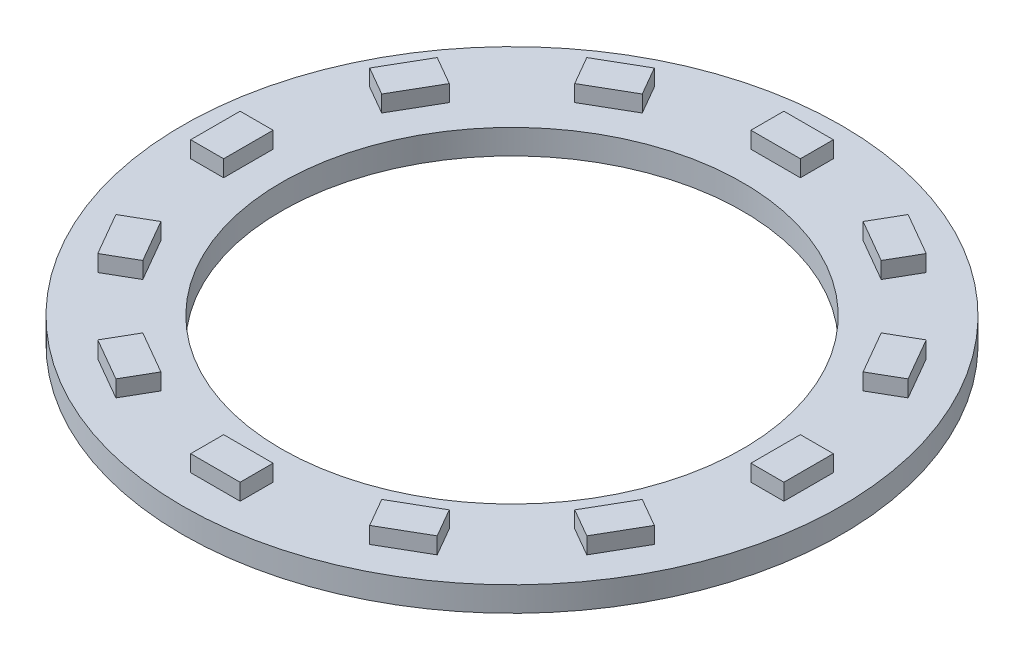
SolidWorks part; units mm, degrees
ref_plane "Front Plane" through (0, 0, 0) normal (0, 0, 1) x (1, 0, 0)
ref_plane "Top Plane" through (0, 0, 0) normal (0, 1, 0) x (1, 0, 0)
ref_plane "Right Plane" through (0, 0, 0) normal (1, 0, 0) x (0, 0, -1)
sketch "Sketch1" plane through (0, 0, 0) normal (0, 1, 0) x (1, 0, 0)
  circle A0 centre (0, 0) radius 20
  circle A1 centre (0, 0) radius 14
  dimension "D1" = 40
  dimension "D2" = 6
extrude "Boss-Extrude1" add sketch "Sketch1" along normal blind 1.5
sketch "Sketch2" plane through (0, 1.5, 0) normal (0, 1, 0) x (1, 0, 0)
  line L0 (0, 0) -> (0, 16) construction
  line L1 (-1.5, 18) -> (1.5, 18)
  line L2 (-1.5, 18) -> (-1.5, 16)
  line L3 (-1.5, 16) -> (1.5, 16)
  line L4 (1.5, 18) -> (1.5, 16)
  dimension "D1" = 16
  dimension "D2" = 3
  dimension "D3" = 2
extrude "Boss-Extrude2" add sketch "Sketch2" along normal blind 1
pattern_circular "CirPattern1" count 12 over 360 about axis through (0, 0, 0) along (0, 1, 0) of "Boss-Extrude2"
